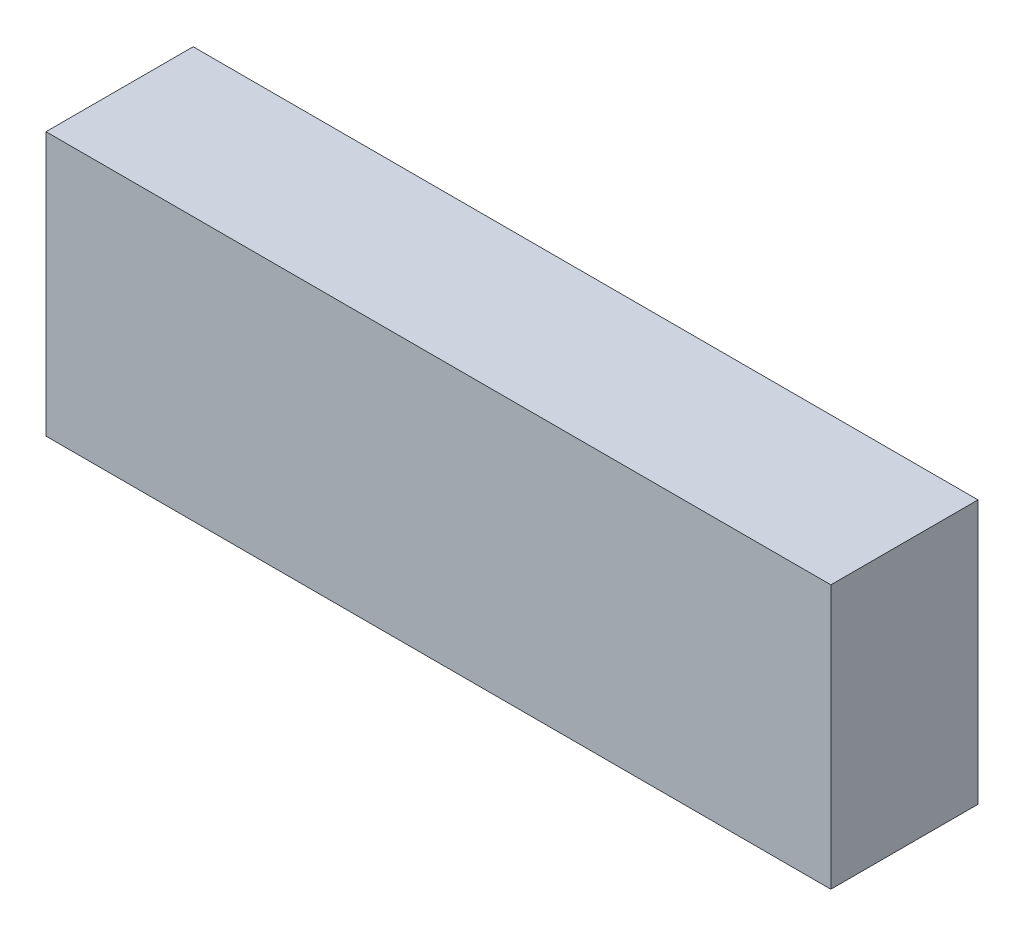
SolidWorks part; units mm, degrees
ref_plane "前视基准面" through (0, 0, 0) normal (0, 0, 1) x (1, 0, 0)
ref_plane "上视基准面" through (0, 0, 0) normal (0, 1, 0) x (1, 0, 0)
ref_plane "右视基准面" through (0, 0, 0) normal (1, 0, 0) x (0, 0, -1)
sketch "草图1" plane through (0, 0, 0) normal (0, 0, 1) x (1, 0, 0)
  line L1 (-64, 21.5) -> (64, 21.5)
  line L2 (-64, 21.5) -> (-64, -21.5)
  line L3 (-64, -21.5) -> (64, -21.5)
  line L4 (64, 21.5) -> (64, -21.5)
  line L5 (-64, 21.5) -> (64, -21.5) construction
  line L6 (-64, -21.5) -> (64, 21.5) construction
  point P0 (0, 0)
  dimension "D1" = 128
  dimension "D2" = 43
extrude "凸台-拉伸1" add sketch "草图1" along normal blind 24
